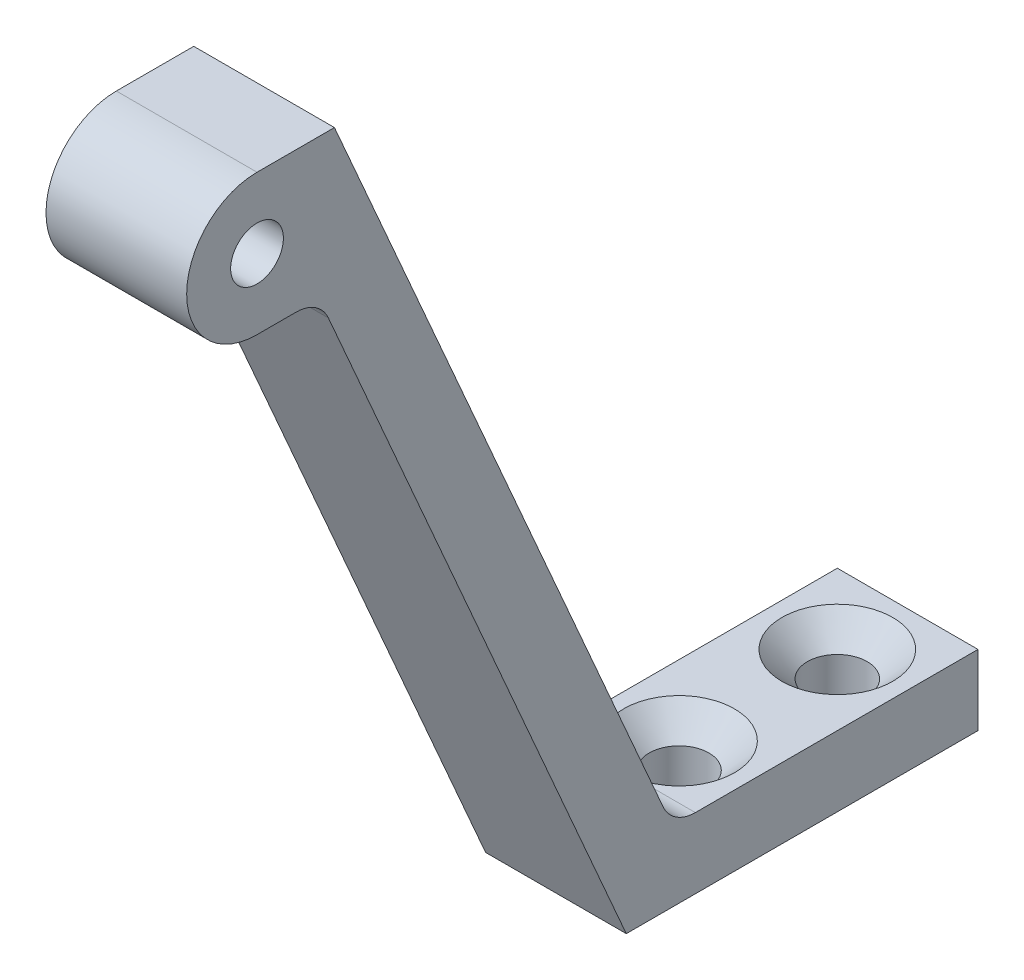
SolidWorks part; units mm, degrees
ref_plane "Front Plane" through (0, 0, 0) normal (0, 0, 1) x (1, 0, 0)
ref_plane "Top Plane" through (0, 0, 0) normal (0, 1, 0) x (1, 0, 0)
ref_plane "Right Plane" through (0, 0, 0) normal (1, 0, 0) x (0, 0, -1)
sketch "Sketch1" plane through (0, 0, 0) normal (1, 0, 0) x (0, 0, -1)
  line L0 (0, 0) -> (0, 3.1172)
  line L1 (0, 3.1172) -> (-17.3821, 3.1172)
  line L2 (-17.3821, 3.1172) -> (-36.5979, 47.1172)
  line L3 (-36.5979, 47.1172) -> (-41, 47.1172)
  line L4 (-41, 39.1172) -> (-37.4689, 39.1172)
  line L5 (-37.4689, 39.1172) -> (-20, -0.8828)
  line L6 (-20, -0.8828) -> (0, -0.8828)
  line L7 (0, -0.8828) -> (0, 3.1172)
  arc A0 (-41, 47.1172) -> (-41, 39.1172) centre (-41, 43.1172) ccw
  circle A1 centre (-41, 43.1172) radius 1.5
  dimension "D6" = 3
  dimension "D7" = 4
  dimension "D1" = 44
  dimension "D2" = 21
  dimension "D3" = 4
  dimension "D4" = 4
  dimension "D5" = 20
extrude "Boss-Extrude1" add sketch "Sketch1" along normal mid plane 8 contours L3 A0 L4 L5 L6 L7 L0 L1 L2 A1
hole_wizard "CSK for M3 Flat Head Machine Screw1" positions "Sketch2" profile "Sketch3" countersink size "M3" standard "ANSI Metric"
sketch "Sketch2" plane through (0, 3.1172, 0) normal (0, 1, 0) x (1, 0, 0)
  line L0 (4, 0) -> (-4, 0) construction
  point P0 (0, -13)
  point P2 (0, -4)
  dimension "D1" = 4
  dimension "D2" = 9
sketch "Sketch3" plane through (0, 3.1172, 13) normal (1, 0, 0) x (0, 0, 1)
  line L0 (0, 0) -> (0, 8.5215)
  line L1 (0, 8.5215) -> (1.7, 7.5)
  line L2 (1.7, 7.5) -> (1.7, 1.45)
  line L3 (1.7, 1.45) -> (3.15, 0)
  line L5 (3.15, 0) -> (0, 0)
  line L6 (-1.7, 1.45) -> (-3.15, 0) construction
  line L10 (0, 8.5215) -> (-1.7, 7.5) construction
  line L11 (0, -6.35) -> (0, 107.95) construction
  dimension "Hole Dia." = 3.4
  dimension "Hole Depth" = 7.5
  dimension "Near C'Sink Dia." = 6.3
  dimension "Near C'Sink Angle" = 90
  dimension "Drill Angle" = 118
fillet "Fillet1" radius 2 2 edges at (0, 39.1172, 37.4689) (0, 3.1172, 17.3821)
